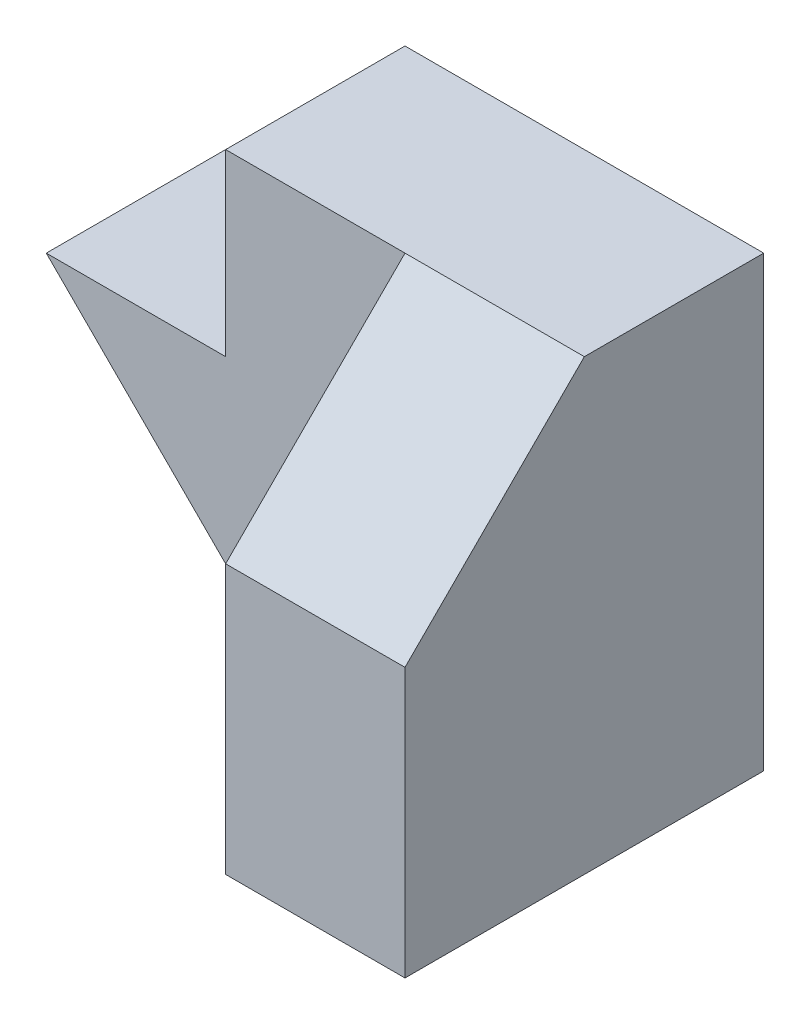
SolidWorks part; units mm, degrees
ref_plane "Front Plane" through (0, 0, 0) normal (0, 0, 1) x (1, 0, 0)
ref_plane "Top Plane" through (0, 0, 0) normal (0, 1, 0) x (1, 0, 0)
ref_plane "Right Plane" through (0, 0, 0) normal (1, 0, 0) x (0, 0, -1)
sketch "Sketch1" plane through (0, 0, 0) normal (0, 0, 1) x (1, 0, 0)
  line L0 (0, 0) -> (15, 0)
  line L1 (15, 0) -> (15, 25)
  line L2 (15, 25) -> (-5, 25)
  line L3 (-5, 25) -> (-5, 15)
  line L4 (-5, 15) -> (-15, 15)
  line L5 (-15, 15) -> (0, 0)
  dimension "D1" = 15
  dimension "D2" = 10
  dimension "D3" = 15
  dimension "D4" = 20
  dimension "D5" = 10
extrude "Boss-Extrude1" add sketch "Sketch1" along normal blind 20
sketch "Sketch2" plane through (0, 0, 20) normal (0, 0, 1) x (1, 0, 0)
  line L0 (5, 25) -> (5, 0)
  line L1 (15, 25) -> (-5, 25) construction
  line L2 (0, 0) -> (15, 0) construction
  line L3 (5, 0) -> (0, 0)
  line L4 (0, 0) -> (-15, 15)
  line L5 (-15, 15) -> (-5, 15)
  line L6 (-5, 15) -> (-5, 25)
  line L7 (-5, 25) -> (5, 25)
  dimension "D1" = 5
extrude "Cut-Extrude1" cut sketch "Sketch2" against normal blind 10
sketch "Sketch3" plane through (5, 0, 0) normal (-1, 0, 0) x (0, 0, 1)
  line L0 (10, 25) -> (20, 25)
  line L1 (20, 25) -> (20, 15)
  line L2 (20, 0) -> (20, 25) construction
  line L3 (20, 15) -> (10, 25)
  dimension "D1" = 10
extrude "Cut-Extrude2" cut sketch "Sketch3" against normal blind 10 contours L3 L0 L1
